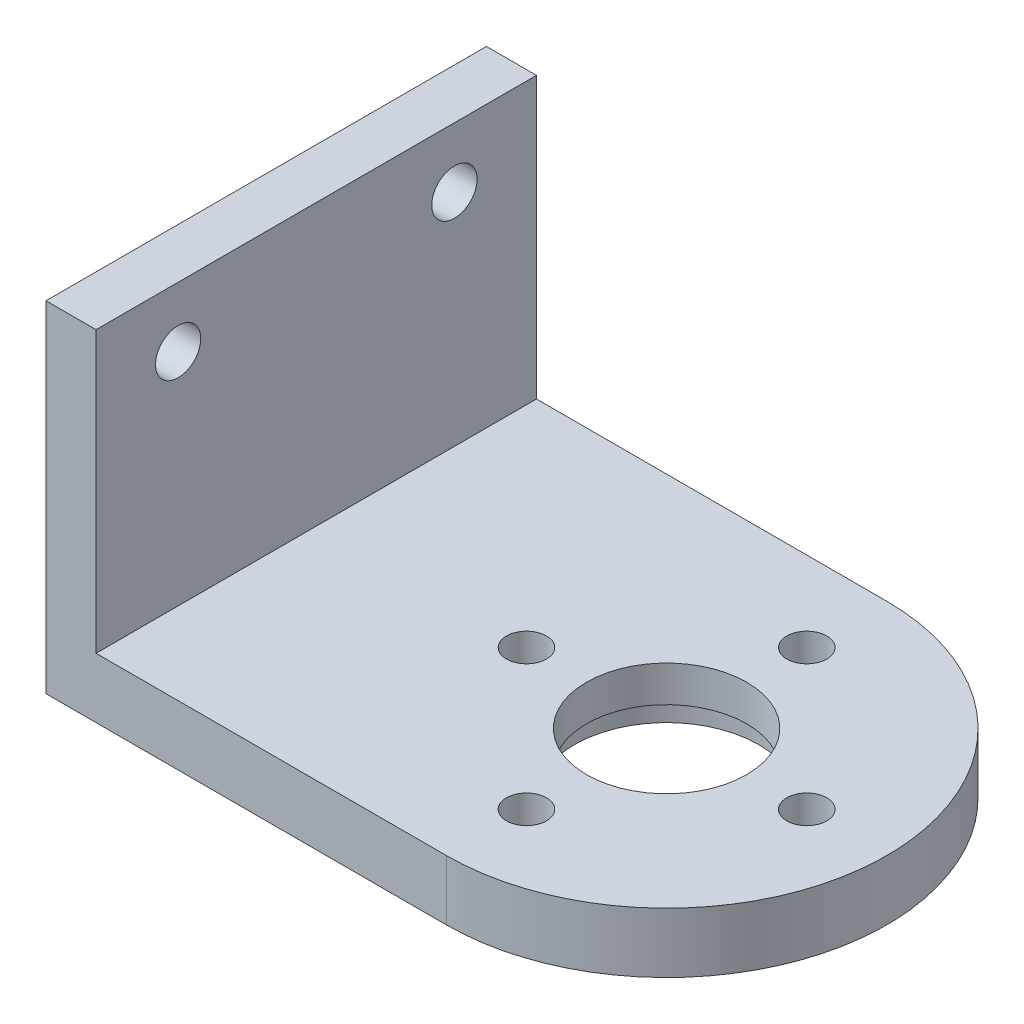
SolidWorks part; units mm, degrees
ref_plane "Front Plane" through (0, 0, 0) normal (0, 0, 1) x (1, 0, 0)
ref_plane "Top Plane" through (0, 0, 0) normal (0, 1, 0) x (1, 0, 0)
ref_plane "Right Plane" through (0, 0, 0) normal (1, 0, 0) x (0, 0, -1)
sketch "Sketch1" plane through (0, 0, 0) normal (0, 1, 0) x (1, 0, 0)
  line L0 (-28.2208, 0) -> (26.2745, 0) construction
  line L2 (-14, -11) -> (-14, 11)
  line L5 (-14, 11) -> (6, 11)
  line L6 (6, -11) -> (-14, -11)
  circle A0 centre (6, -7) radius 1
  circle A1 centre (-1, 0) radius 1
  circle A2 centre (6, 0) radius 4
  arc A3 (6, -11) -> (6, 11) centre (6, 0) ccw
  circle A4 centre (13, 0) radius 1
  circle A5 centre (6, 7) radius 1
  point P0 (0, 0)
  point P6 (-14, 0)
  point P22 (6, 0)
  dimension "D3" = 8
  dimension "D5" = 22
  dimension "D6" = 4
  dimension "D12" = 2
  dimension "D2" = 22
  dimension "D4" = 20
  dimension "D11" = 7
extrude "Boss-Extrude1" add sketch "Sketch1" along normal blind 3
sketch "Sketch2" plane through (0, 3, 0) normal (0, 1, 0) x (1, 0, 0)
  line L0 (-14, 11) -> (-11.5, 11)
  line L1 (6, 11) -> (-14, 11) construction
  line L2 (-11.5, 11) -> (-11.5, -11)
  line L3 (-14, -11) -> (6, -11) construction
  line L4 (-11.5, -11) -> (-14, -11)
  line L5 (-14, 11) -> (-14, -11)
  dimension "D1" = 2.5
extrude "Boss-Extrude2" add sketch "Sketch2" along normal blind 14
sketch "Sketch3" plane through (-11.5, 0, 0) normal (1, 0, 0) x (0, 0, -1)
  line L0 (11, 17) -> (11, 3) construction
  line L1 (-11, 17) -> (11, 17) construction
  line L2 (-11, 17) -> (-11, 3) construction
  circle A0 centre (6.9, 14) radius 1.1324
  circle A1 centre (-6.9, 14) radius 1.131
  point P6 (11, 10)
  point P11 (-11, 10)
  dimension "D1" = 4.1
  dimension "D2" = 3
  dimension "D3" = 4.1
  dimension "D4" = 3
extrude "Cut-Extrude1" cut sketch "Sketch3" against normal blind 6
sketch "Sketch4" plane through (0, 0, 0) normal (0, -1, 0) x (1, 0, 0)
  circle A0 centre (6, 0) radius 4.6
  dimension "D1" = 9.2
extrude "Cut-Extrude2" cut sketch "Sketch4" against normal blind 1.2
sketch "Sketch5" plane through (0, 0, 0) normal (0, -1, 0) x (1, 0, 0)
  circle A0 centre (13, 0) radius 1.9
  circle A1 centre (6, -7) radius 1.9
  circle A2 centre (-1, 0) radius 1.9
  circle A3 centre (6, 7) radius 1.9
  point P12 (6, 0)
  dimension "D1" = 3.8
  dimension "D2" = 4
extrude "Cut-Extrude3" cut sketch "Sketch5" against normal blind 1.5
